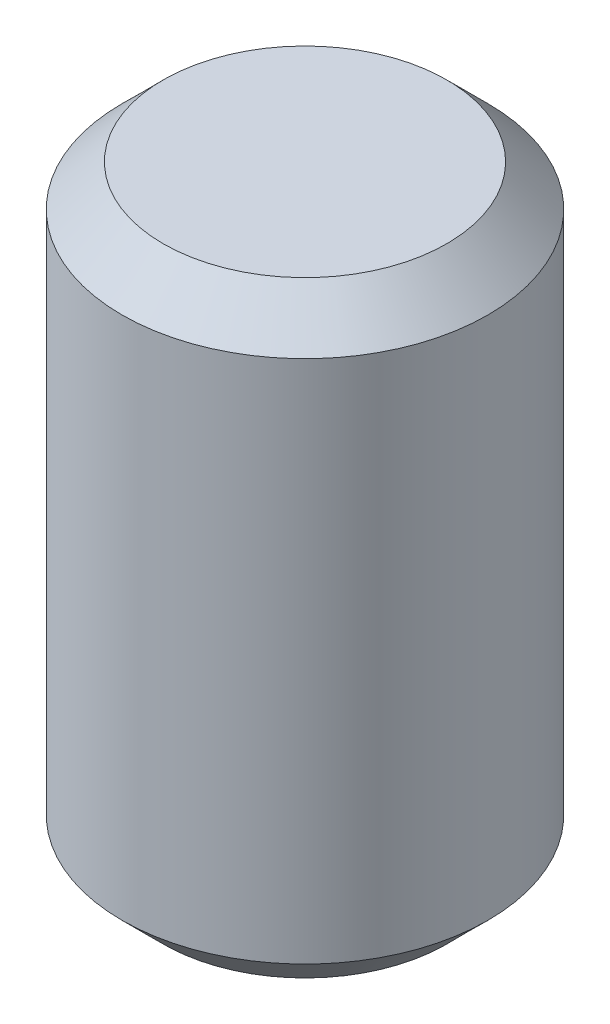
SolidWorks part; units mm, degrees
material "Alloy Steel"
ref_plane "Front Plane" through (0, 0, 0) normal (0, 0, 1) x (1, 0, 0)
ref_plane "Top Plane" through (0, 0, 0) normal (0, 1, 0) x (1, 0, 0)
ref_plane "Right Plane" through (0, 0, 0) normal (1, 0, 0) x (0, 0, -1)
ref_plane "Plane1" through (0, 0, 0) normal (0, 0, -1) x (-1, 0, 0)
sketch "Sketch1" plane through (0, 0, 0) normal (0, 0, -1) x (-1, 0, 0)
  line L0 (-0.89, 0) -> (0, 0)
  line L1 (0, 0) -> (0, 2.95)
  line L2 (0, 2.95) -> (-0.89, 2.95)
  line L3 (-0.89, 2.95) -> (-0.89, 0)
  line L4 (0, 0) -> (0, 2.95) construction
revolve "Revolve1" add sketch "Sketch1" angle 360 about L4
sketch "Sketch2" plane through (0, 0, 0) normal (0, -1, 0) x (1, 0, 0)
  line L0 (-0.235, 0.407) -> (-0.47, 0)
  line L1 (-0.47, 0) -> (-0.235, -0.407)
  line L2 (-0.235, -0.407) -> (0.235, -0.407)
  line L3 (0.235, -0.407) -> (0.47, 0)
  line L4 (0.47, 0) -> (0.235, 0.407)
  line L5 (0.235, 0.407) -> (-0.235, 0.407)
extrude "Cut-Extrude1" cut sketch "Sketch2" against normal blind 0.375
chamfer "Chamfer1" distance 0.2 angle 45 2 edges at (0, 0, 0.89) (0, 2.95, 0.89)
